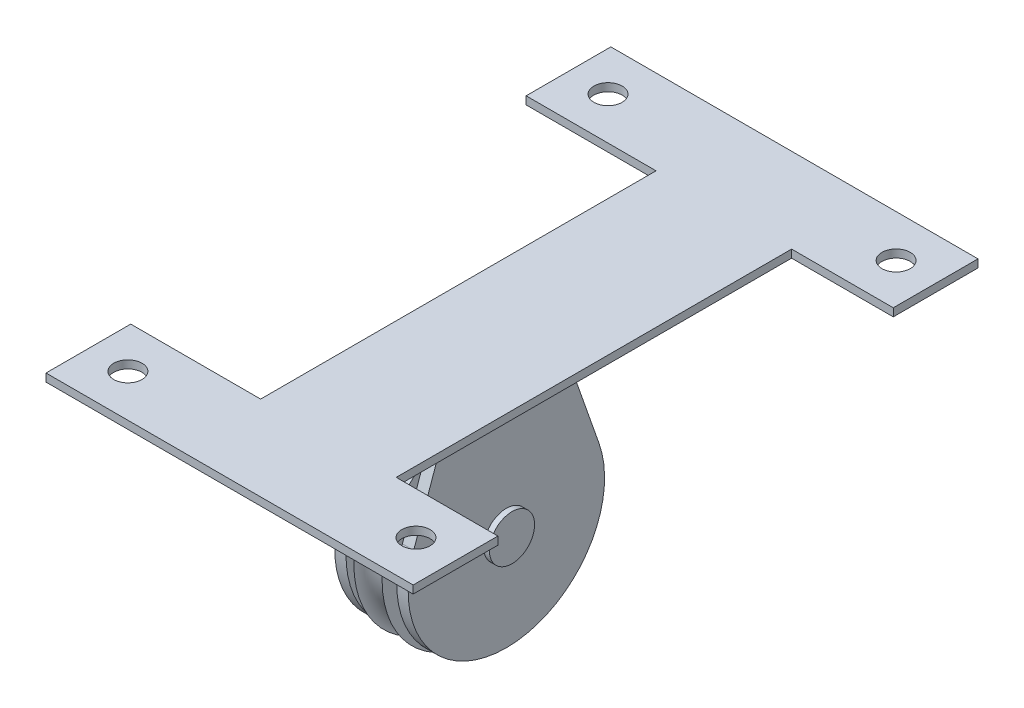
SolidWorks part; units mm, degrees
material "6061-T6 (SS)"
ref_plane "Front Plane" through (0, 0, 0) normal (0, 0, 1) x (1, 0, 0)
ref_plane "Top Plane" through (0, 0, 0) normal (0, 1, 0) x (1, 0, 0)
ref_plane "Right Plane" through (0, 0, 0) normal (1, 0, 0) x (0, 0, -1)
sketch "Sketch1" plane through (0, 0, 0) normal (0, 0, 1) x (1, 0, 0)
  line L5 (0, 0) -> (0, 5.08) construction
  line L7 (-3.175, 5.08) -> (3.175, 5.08)
  line L8 (-3.175, 5.08) -> (-3.175, 22.86)
  line L9 (3.175, 5.08) -> (3.175, 22.86)
  line L10 (0, 0) -> (10.0479, 0) construction
  arc A1 (-3.175, 22.86) -> (3.175, 22.86) centre (0, 22.86) ccw
  point P5 (0, 5.08)
  dimension "D1" = 6.35
  dimension "D2" = 17.78
revolve "Revolve1" add sketch "Sketch1" angle 360 about L10
ref_plane "Plane1" through (5.715, 0, 0) normal (1, 0, 0) x (0, 0, -1)
sketch "Sketch2" plane through (5.715, 0, 0) normal (1, 0, 0) x (0, 0, -1)
  line L0 (-20.8365, 7.3204) -> (-12.7, 30.48)
  line L1 (0, 0) -> (0, 30.48) construction
  line L2 (12.7, 30.48) -> (-12.7, 30.48)
  line L3 (20.8365, 7.3204) -> (12.7, 30.48)
  arc A0 (-20.8365, 7.3204) -> (20.8365, 7.3204) centre (0, 0) ccw
  circle A2 centre (0, 0) radius 5.08
  dimension "D1" = 30.48
  dimension "D2" = 25.4
extrude "Boss-Extrude1" add sketch "Sketch2" along normal blind 2.54
mirror "Mirror2" about plane through (0, 0, 0) normal (1, 0, 0) of bodies 102
sketch "Sketch3" plane through (0, 30.48, 0) normal (0, 1, 0) x (1, 0, 0)
  line L6 (15.24, 57.15) -> (15.24, -31.75)
  line L21 (-15.24, 57.15) -> (-15.24, -31.75)
  line L24 (0, 0) -> (0, -50.8) construction
  line L25 (38.1, -41.275) -> (0, -41.275) construction
  line L28 (15.24, -31.75) -> (38.1, -31.75)
  line L29 (38.1, -50.8) -> (38.1, -31.75)
  line L30 (15.24, 0) -> (-15.24, 0) construction
  line L31 (15.24, -31.75) -> (-15.24, -31.75) construction
  line L33 (-44.45, -50.8) -> (-44.45, -31.75)
  line L34 (-44.45, -31.75) -> (-15.24, -31.75)
  line L35 (0, -41.275) -> (-44.45, -41.275) construction
  line L36 (7.8812, 76.2) -> (7.8812, -50.8) construction
  line L37 (7.8812, 12.7) -> (76.3318, 12.7) construction
  line L38 (-44.45, 57.15) -> (-15.24, 57.15)
  line L39 (-44.45, 76.2) -> (-44.45, 57.15)
  line L42 (38.1, 76.2) -> (38.1, 57.15)
  line L43 (15.24, 57.15) -> (38.1, 57.15)
  line L44 (38.1, -50.8) -> (-44.45, -50.8)
  line L45 (38.1, 76.2) -> (-44.45, 76.2)
  dimension "D1" = 38.1
  dimension "D2" = 30.48
  dimension "D3" = 19.05
  dimension "D4" = 44.45
extrude "Boss-Extrude2" add sketch "Sketch3" against normal blind 1.778
sketch "Sketch4" plane through (0, 28.702, 0) normal (0, -1, 0) x (-1, 0, 0)
  line L0 (-38.1, -41.275) -> (-29.21, -41.275) construction
  line L2 (-38.1, -50.8) -> (-38.1, -31.75) construction
  line L4 (3.175, -50.8) -> (3.175, 76.2) construction
  line L5 (44.45, -50.8) -> (-38.1, -50.8) construction
  line L6 (-38.1, 76.2) -> (44.45, 76.2) construction
  line L7 (3.175, 12.7) -> (44.3583, 12.7) construction
  circle A10 centre (-29.21, -41.275) radius 3.175
  circle A11 centre (35.56, -41.275) radius 3.175
  circle A12 centre (-29.21, 66.675) radius 3.175
  circle A13 centre (35.56, 66.675) radius 3.175
  dimension "D1" = 8.89
  dimension "D2" = 6.35
extrude "Cut-Extrude2" cut sketch "Sketch4" against normal through all
sketch "Sketch6" plane through (0, 0, 0) normal (1, 0, 0) x (0, 0, -1)
  circle A1 centre (0, 0) radius 5.08
extrude "Boss-Extrude4" add sketch "Sketch6" along normal mid plane 19.05
